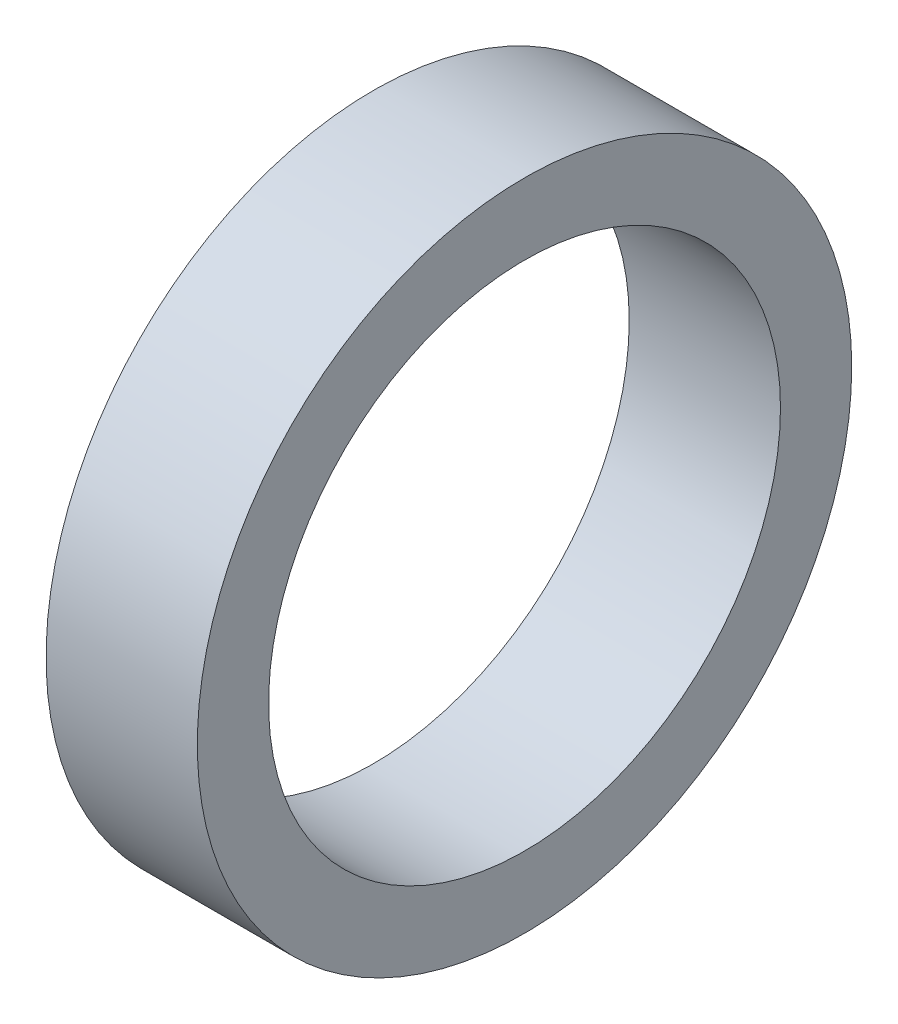
SolidWorks part; units mm, degrees
ref_plane "Front" through (0, 0, 0) normal (0, 0, 1) x (1, 0, 0)
ref_plane "Top" through (0, 0, 0) normal (0, 1, 0) x (1, 0, 0)
ref_plane "Right" through (0, 0, 0) normal (1, 0, 0) x (0, 0, -1)
sketch "Sketch1" plane through (0, 0, 0) normal (1, 0, 0) x (0, 0, -1)
  circle A0 centre (0, 0) radius 11.176
  circle A1 centre (0, 0) radius 14.2875
  dimension "D1" = 28.575
  dimension "D2" = 22.352
extrude "Boss-Extrude1" add sketch "Sketch1" along normal blind 6.604
